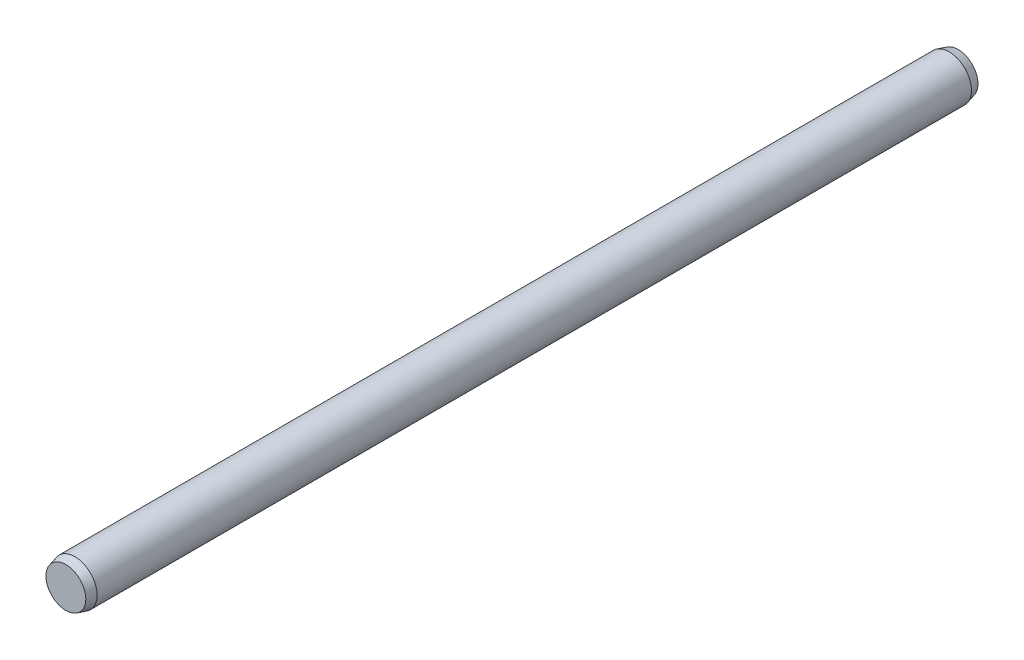
SolidWorks part; units mm, degrees
ref_plane "Front Plane" through (0, 0, 0) normal (0, 0, 1) x (1, 0, 0)
ref_plane "Top Plane" through (0, 0, 0) normal (0, 1, 0) x (1, 0, 0)
ref_plane "Right Plane" through (0, 0, 0) normal (1, 0, 0) x (0, 0, -1)
sketch "Sketch1" plane through (0, 0, 0) normal (1, 0, 0) x (0, 0, -1)
  line L0 (-10, 0) -> (10, 0)
  dimension "Length" = 20
sketch "Sketch2" plane through (0, 0, 0) normal (0, 0, 1) x (1, 0, 0)
  circle A0 centre (0, 0) radius 0.5
  dimension "Diameter" = 1
sketch "Sketch3" plane through (0, 0, 0) normal (1, 0, 0) x (0, 0, -1)
  line L0 (-10, 0) -> (-10, 0.4464)
  line L1 (-10, 0.4464) -> (-9.8, 0.5)
  line L2 (-9.8, 0.5) -> (9.8, 0.5)
  line L5 (10, 0) -> (-10, 0)
  line L6 (-10, 0) -> (10, 0) construction
  line L7 (-10, 0) -> (10, 0) construction
  line L8 (9.8, 0.5) -> (10, 0.4464)
  line L9 (10, 0.4464) -> (10, 0)
  point P0 (0, 0.5)
  dimension "D1" = 15
  dimension "Point Height" = 0.2
revolve "Revolve1" add sketch "Sketch3" angle 360 about L0
